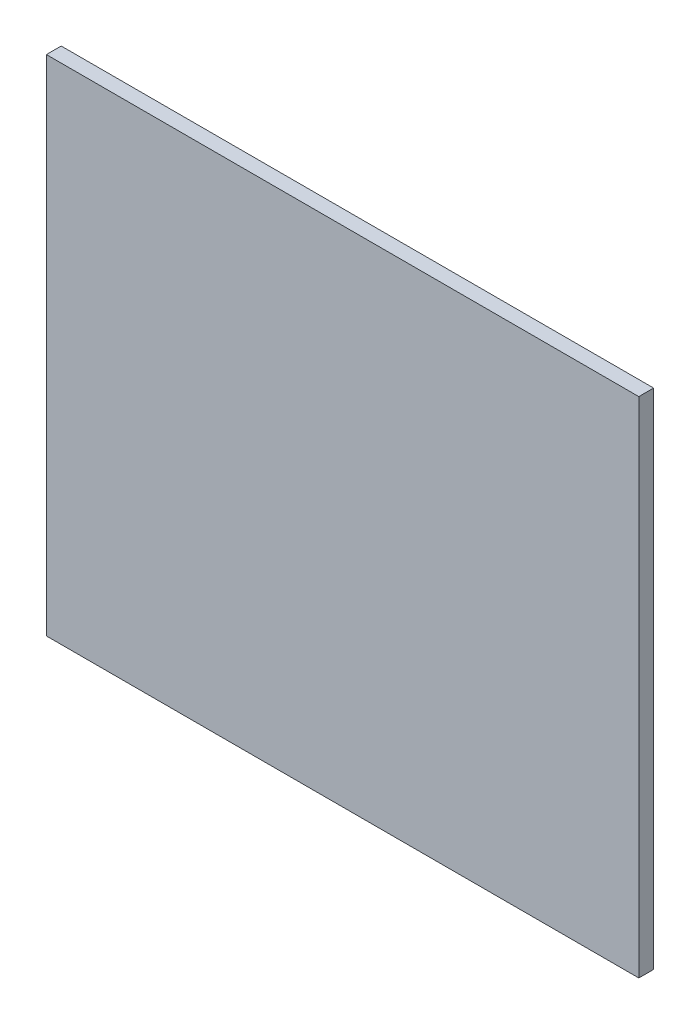
SolidWorks part; units mm, degrees
material "PET"
ref_plane "Plano frontal" through (0, 0, 0) normal (0, 0, 1) x (1, 0, 0)
ref_plane "Plano superior" through (0, 0, 0) normal (0, 1, 0) x (1, 0, 0)
ref_plane "Plano direito" through (0, 0, 0) normal (1, 0, 0) x (0, 0, -1)
sketch "Esboço1" plane through (0, 0, 0) normal (0, 0, 1) x (1, 0, 0)
  line L0 (39.98, 32.89) -> (39.98, -0.01) construction
  line L1 (0, 0) -> (39.98, 0)
  line L2 (0, 0) -> (0, 33.98)
  line L3 (0, 33.98) -> (39.98, 33.98)
  line L4 (39.98, 0) -> (39.98, 33.98)
  line L5 (38.99, 33.98) -> (0.99, 33.98) construction
extrude "Ressalto-extrusão1" add sketch "Esboço1" along normal blind 1
